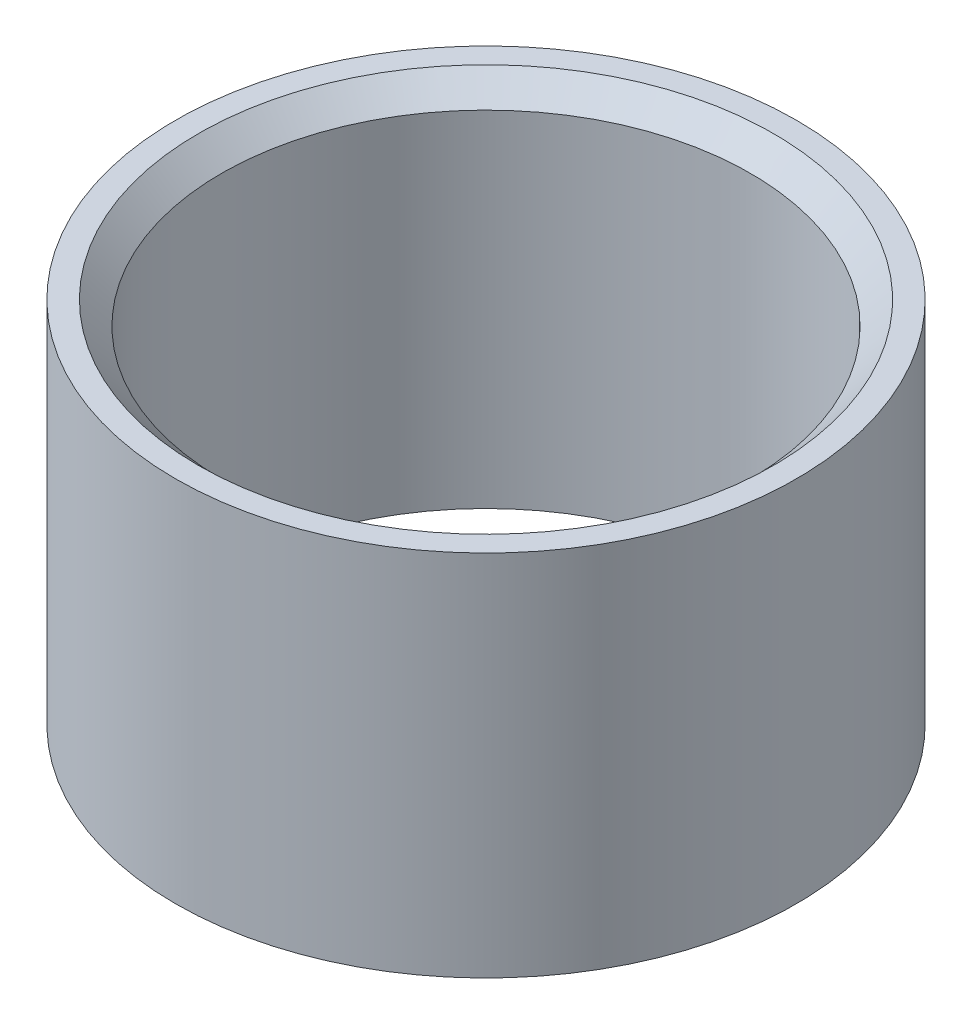
SolidWorks part; units mm, degrees
ref_plane "Front Plane" through (0, 0, 0) normal (0, 0, 1) x (1, 0, 0)
ref_plane "Top Plane" through (0, 0, 0) normal (0, 1, 0) x (1, 0, 0)
ref_plane "Right Plane" through (0, 0, 0) normal (1, 0, 0) x (0, 0, -1)
sketch "Sketch1" plane through (0, 0, 0) normal (0, 1, 0) x (1, 0, 0)
  circle A0 centre (0, 0) radius 1.35
  dimension "D1" = 2.7
extrude "Boss-Extrude1" add sketch "Sketch1" along normal blind 1.6
sketch "Sketch2" plane through (0, 1.6, 0) normal (0, 1, 0) x (1, 0, 0)
  circle A0 centre (0, 0) radius 1.15
  dimension "D1" = 2.3
extrude "Cut-Extrude1" cut sketch "Sketch2" against normal through all
chamfer "Chamfer1" distance 0.1 angle 45 1 edges at (0, 1.6, 1.15)
